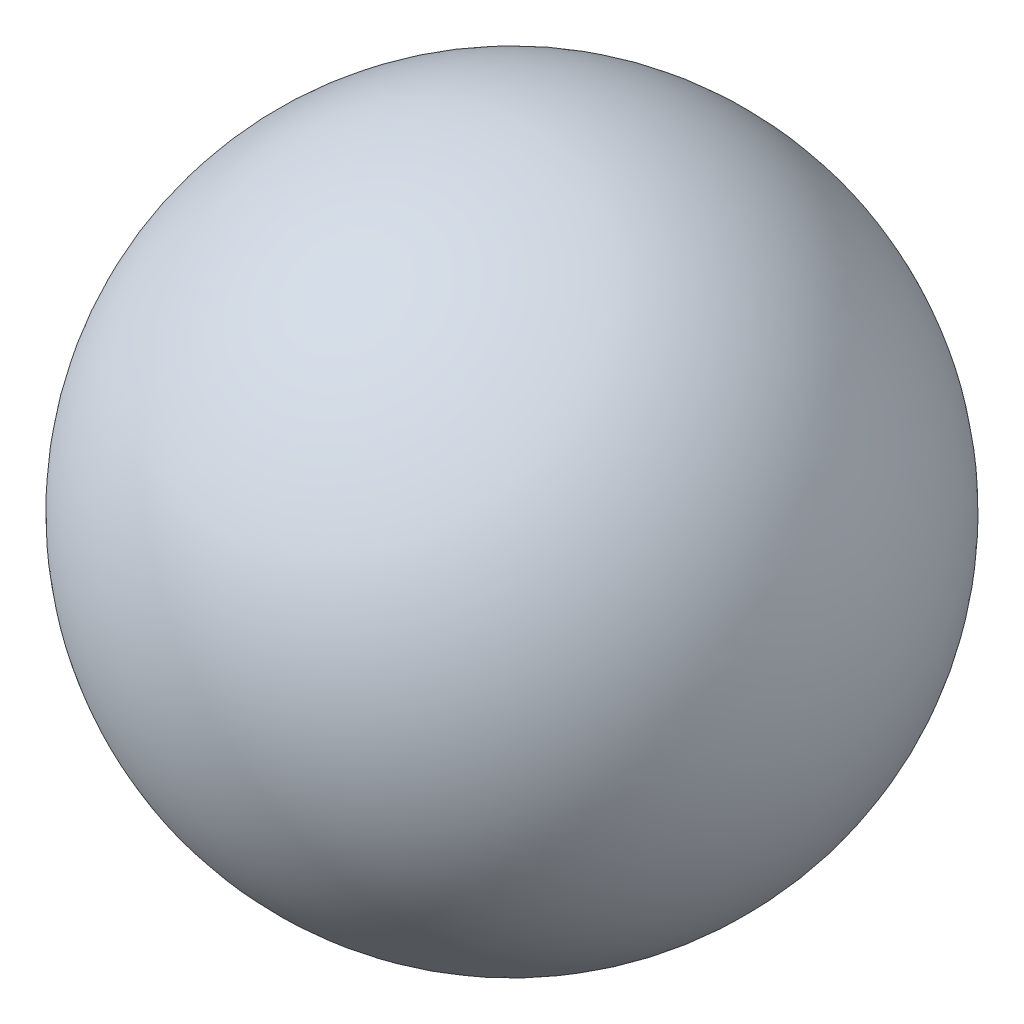
SolidWorks part; units mm, degrees
ref_plane "前视基准面" through (0, 0, 0) normal (0, 0, 1) x (1, 0, 0)
ref_plane "上视基准面" through (0, 0, 0) normal (0, 1, 0) x (1, 0, 0)
ref_plane "右视基准面" through (0, 0, 0) normal (1, 0, 0) x (0, 0, -1)
sketch "草图1" plane through (0, 0, 0) normal (0, 1, 0) x (1, 0, 0)
  line L0 (0, 6.9361) -> (0, -4.0328) construction
  circle A0 centre (0, 0) radius 4
  dimension "D1" = 8
revolve "旋转2" add sketch "草图1" angle 360 about L0
